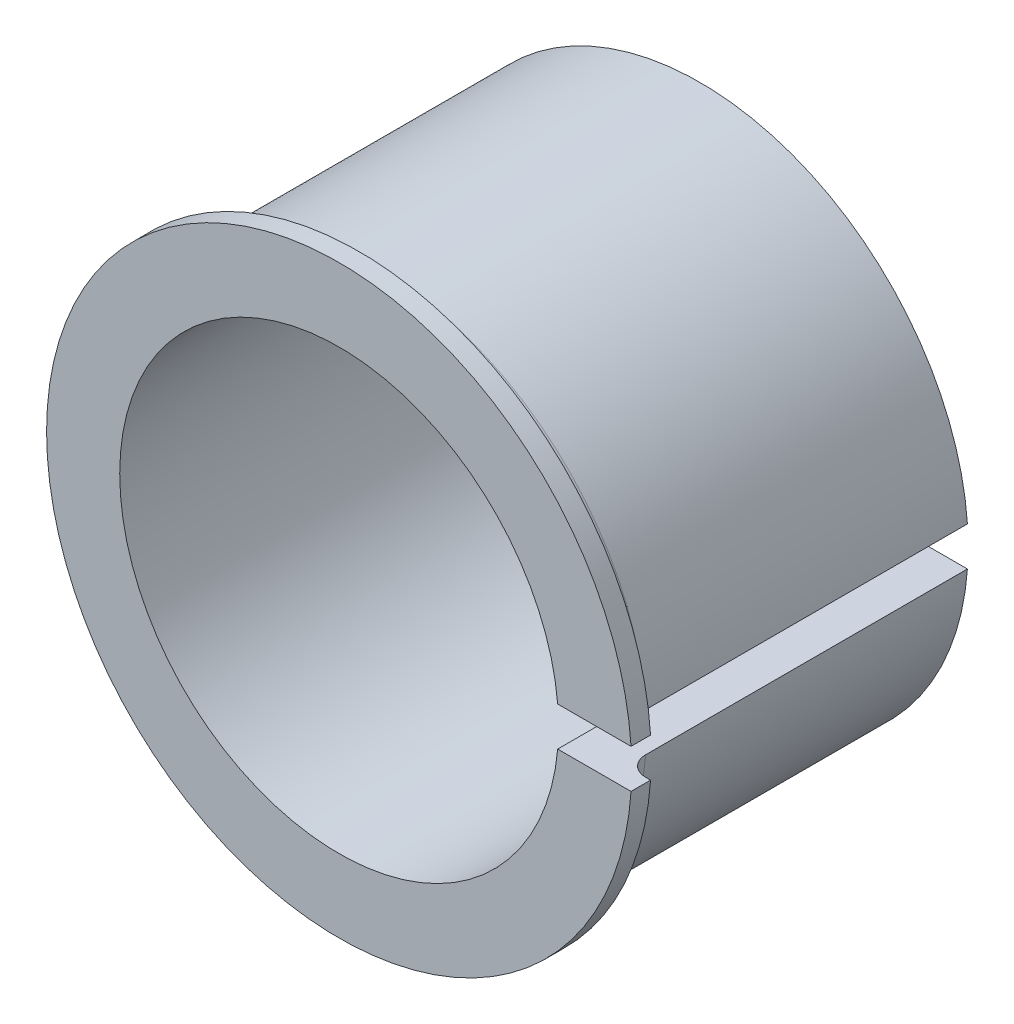
SolidWorks part; units mm, degrees
ref_plane "Front" through (0, 0, 0) normal (0, 0, 1) x (1, 0, 0)
ref_plane "Top" through (0, 0, 0) normal (0, 1, 0) x (1, 0, 0)
ref_plane "Right" through (0, 0, 0) normal (1, 0, 0) x (0, 0, -1)
sketch "Эскиз1" plane through (0, 0, 0) normal (0, 0, 1) x (1, 0, 0)
  line L1 (22.4109, 2) -> (27.4272, 2)
  line L3 (22.4109, -2) -> (27.4272, -2)
  arc A0 (22.4109, 2) -> (22.4109, -2) centre (0, 0) ccw
  arc A1 (27.4272, 2) -> (27.4272, -2) centre (0, 0) ccw
  point P4 (24.8399, 0)
  dimension "D1" = 45
  dimension "D2" = 55
extrude "Бобышка-Вытянуть1" add sketch "Эскиз1" along normal blind 35
sketch "Эскиз2" plane through (0, 0, 35) normal (0, 0, 1) x (1, 0, 0)
  line L0 (22.4109, 2) -> (29.9333, 2)
  line L1 (22.4109, -2) -> (29.9333, -2)
  arc A0 (22.4109, 2) -> (22.4109, -2) centre (0, 0) ccw
  arc A1 (29.9333, 2) -> (29.9333, -2) centre (0, 0) ccw
extrude "Бобышка-Вытянуть2" add sketch "Эскиз2" along normal blind 2
fillet "Скругление1" radius 2 1 edges
